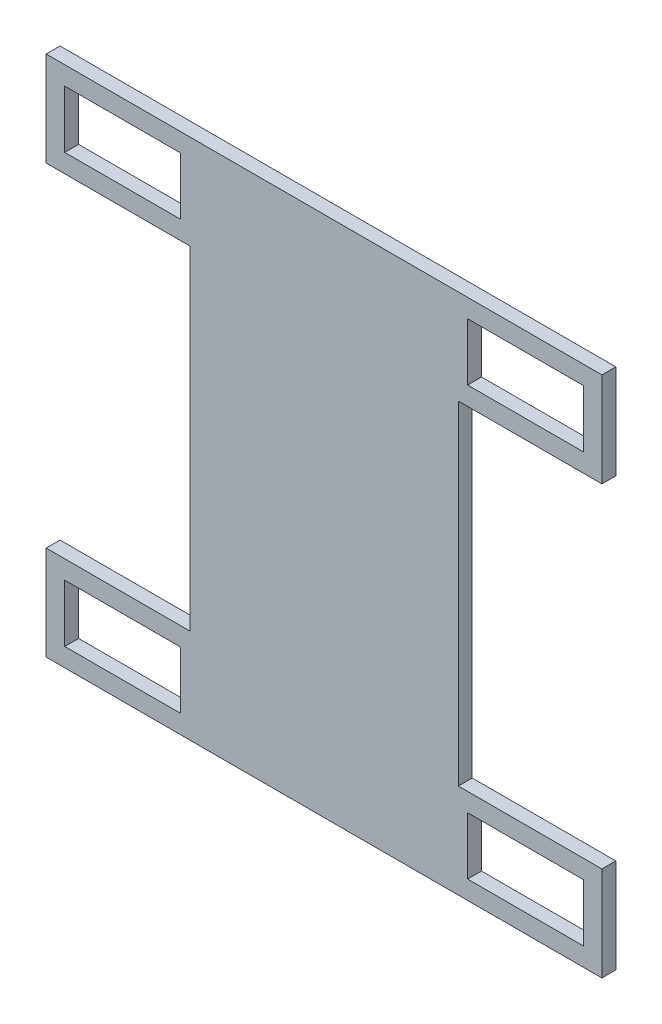
SolidWorks part; units mm, degrees
material "Teca"
ref_plane "Front Plane" through (0, 0, 0) normal (0, 0, 1) x (1, 0, 0)
ref_plane "Top Plane" through (0, 0, 0) normal (0, 1, 0) x (1, 0, 0)
ref_plane "Right Plane" through (0, 0, 0) normal (1, 0, 0) x (0, 0, -1)
sketch "Esboço1" plane through (0, 0, 0) normal (0, 0, 1) x (1, 0, 0)
  line L0 (0, -918.5956) -> (0, 45011.1844) construction
  line L1 (-60, 56.4) -> (60, 56.4)
  line L2 (60, 56.4) -> (60, 36)
  line L3 (60, 36) -> (29, 36)
  line L4 (29, 36) -> (29, -36)
  line L5 (29, -36) -> (60, -36)
  line L6 (60, -36) -> (60, -56.4)
  line L7 (60, -56.4) -> (-60, -56.4)
  line L8 (-60, -36) -> (-60, -56.4)
  line L9 (-29, -36) -> (-60, -36)
  line L10 (-29, 36) -> (-29, -36)
  line L11 (-60, 36) -> (-29, 36)
  line L12 (-60, 56.4) -> (-60, 36)
  line L13 (-1000, 0) -> (49000, 0) construction
  line L14 (31, 52.4) -> (56, 52.4)
  line L15 (31, 52.4) -> (31, 40)
  line L16 (31, 40) -> (56, 40)
  line L17 (56, 52.4) -> (56, 40)
  line L18 (43.5, 40) -> (43.5, 52.4) construction
  line L19 (31, 46.2) -> (56, 46.2) construction
  line L20 (31, -40) -> (56, -40)
  line L21 (56, -52.4) -> (56, -40)
  line L22 (31, -52.4) -> (31, -40)
  line L23 (31, -52.4) -> (56, -52.4)
  line L24 (-56, -52.4) -> (-56, -40)
  line L25 (-31, -52.4) -> (-56, -52.4)
  line L26 (-31, -52.4) -> (-31, -40)
  line L27 (-31, -40) -> (-56, -40)
  line L28 (-31, 40) -> (-56, 40)
  line L29 (-56, 52.4) -> (-56, 40)
  line L30 (-31, 52.4) -> (-31, 40)
  line L31 (-31, 52.4) -> (-56, 52.4)
  point P1 (43.5, 46.2)
  point P12 (0, -56.4)
  point P17 (0, 56.4)
  dimension "D1" = 20.4
  dimension "D2" = 72
  dimension "D3" = 120
  dimension "D4" = 29
  dimension "D5" = 25
  dimension "D6" = 12.4
  dimension "D7" = 4
  dimension "D8" = 36
  dimension "D9" = 4
extrude "Ressalto-extrusão1" add sketch "Esboço1" along normal blind 3
